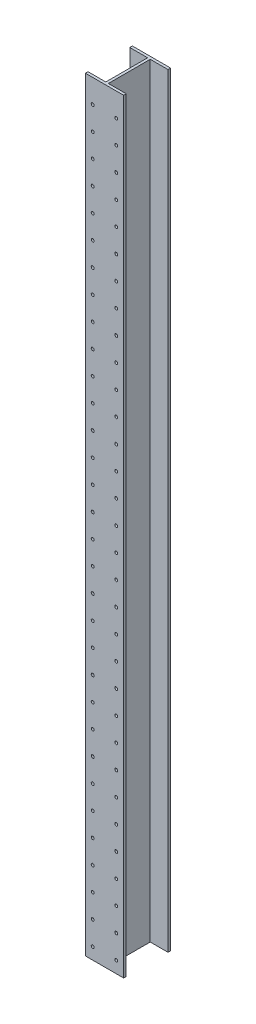
SolidWorks part; units mm, degrees
ref_plane "Front Plane" through (0, 0, 0) normal (0, 0, 1) x (1, 0, 0)
ref_plane "Top Plane" through (0, 0, 0) normal (0, 1, 0) x (1, 0, 0)
ref_plane "Right Plane" through (0, 0, 0) normal (1, 0, 0) x (0, 0, -1)
sketch "Sketch1" plane through (0, 0, 0) normal (0, 1, 0) x (1, 0, 0)
  line L0 (-5.588, 90.424) -> (5.588, 90.424) construction
  line L1 (-5.588, -90.424) -> (5.588, -90.424) construction
  line L2 (-5.588, -90.424) -> (-5.588, 90.424)
  line L3 (-5.588, 90.424) -> (5.588, 90.424) construction
  line L4 (5.588, -90.424) -> (5.588, 90.424)
  line L5 (-5.588, -90.424) -> (5.588, 90.424) construction
  line L6 (-5.588, 90.424) -> (5.588, -90.424) construction
  line L7 (-82.55, 90.424) -> (-5.588, 90.424)
  line L8 (-82.55, 90.424) -> (-82.55, 101.6)
  line L9 (-82.55, 101.6) -> (82.55, 101.6)
  line L10 (82.55, 90.424) -> (82.55, 101.6)
  line L11 (-82.55, -101.6) -> (82.55, -101.6)
  line L12 (-82.55, -101.6) -> (-82.55, -90.424)
  line L13 (-82.55, -90.424) -> (-5.588, -90.424)
  line L14 (82.55, -101.6) -> (82.55, -90.424)
  line L15 (5.588, 90.424) -> (82.55, 90.424)
  line L16 (-5.588, -90.424) -> (5.588, -90.424) construction
  line L17 (5.588, -90.424) -> (82.55, -90.424)
  point P0 (0, 0)
  point P14 (0, 0)
  point P15 (0, 0)
  point P16 (0, 0)
  point P17 (-31.3938, -25.4404)
  point P19 (35.1069, -17.7605)
  dimension "D1" = 11.176
  dimension "D2" = 165.1
  dimension "D3" = 11.176
  dimension "D4" = 203.2
extrude "Boss-Extrude1" add sketch "Sketch1" along normal blind 3302
sketch "Sketch2" plane through (0, 0, 101.6) normal (0, 0, 1) x (1, 0, 0)
  line L0 (0, 0) -> (0, -36.697) construction
  circle A0 centre (-50.8, 50.8) radius 6.35
  circle A1 centre (50.8, 50.8) radius 6.35
  point P5 (0, -36.697)
  dimension "D1" = 12.7
  dimension "D2" = 50.8
  dimension "D3" = 50.8
extrude "Cut-Extrude1" cut sketch "Sketch2" against normal up to next (11.176 mm away)
pattern_linear "LPattern1" count 32 spacing 101.6 along (0, 1, 0) of "Cut-Extrude1"
